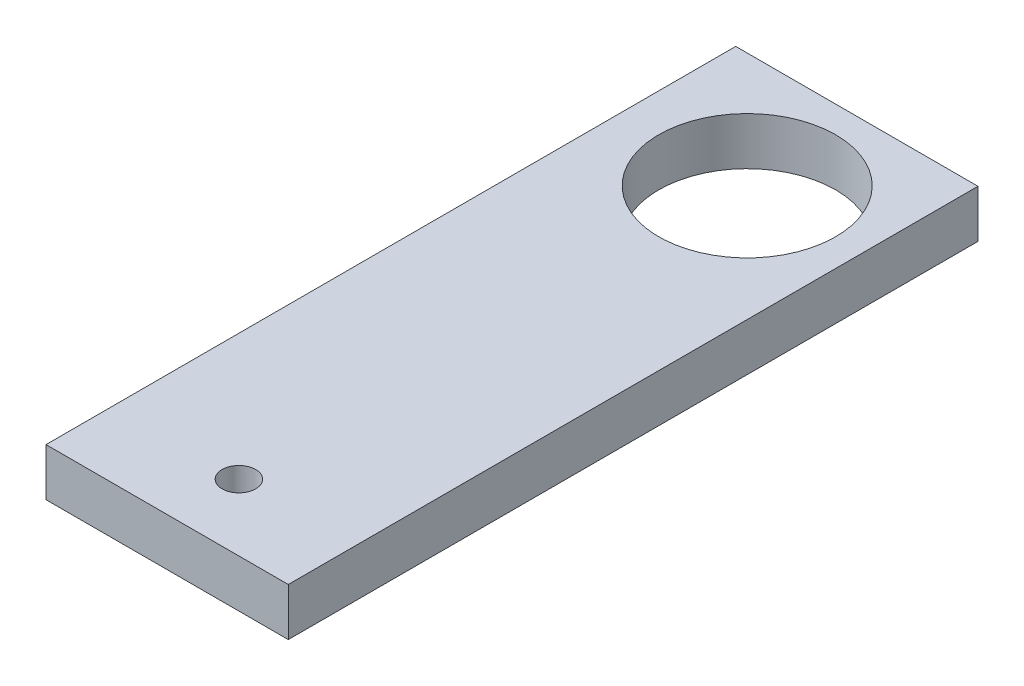
SolidWorks part; units mm, degrees
ref_plane "Front Plane" through (0, 0, 0) normal (0, 0, 1) x (1, 0, 0)
ref_plane "Top Plane" through (0, 0, 0) normal (0, 1, 0) x (1, 0, 0)
ref_plane "Right Plane" through (0, 0, 0) normal (1, 0, 0) x (0, 0, -1)
sketch "Sketch1" plane through (0, 0, 0) normal (0, 1, 0) x (1, 0, 0)
  line L1 (-3.574, 9.75) -> (3.276, 9.75)
  line L2 (-3.574, 9.75) -> (-3.574, -9.75)
  line L3 (-3.574, -9.75) -> (3.276, -9.75)
  line L4 (3.276, 9.75) -> (3.276, -9.75)
  point P0 (0, 0)
  dimension "D1" = 19.5
  dimension "D2" = 6.85
extrude "Boss-Extrude2" add sketch "Sketch1" along normal blind 1.35
sketch "Sketch2" plane through (0, 0, 0) normal (0, -1, 0) x (1, 0, 0)
  line L0 (3.276, -9.75) -> (-3.574, -9.75) construction
  circle A0 centre (0, -6.5) radius 2.5
  dimension "D1" = 5
  dimension "D2" = 3.25
extrude "Cut-Extrude1" cut sketch "Sketch2" against normal blind 1.35
sketch "Sketch3" plane through (0, 1.35, 0) normal (0, 1, 0) x (1, 0, 0)
  line L0 (-3.574, -9.75) -> (3.276, -9.75) construction
  circle A0 centre (0, -7.87) radius 0.475
  dimension "D1" = 0.95
  dimension "D2" = 1.88
extrude "Cut-Extrude2" cut sketch "Sketch3" against normal blind 1.35
